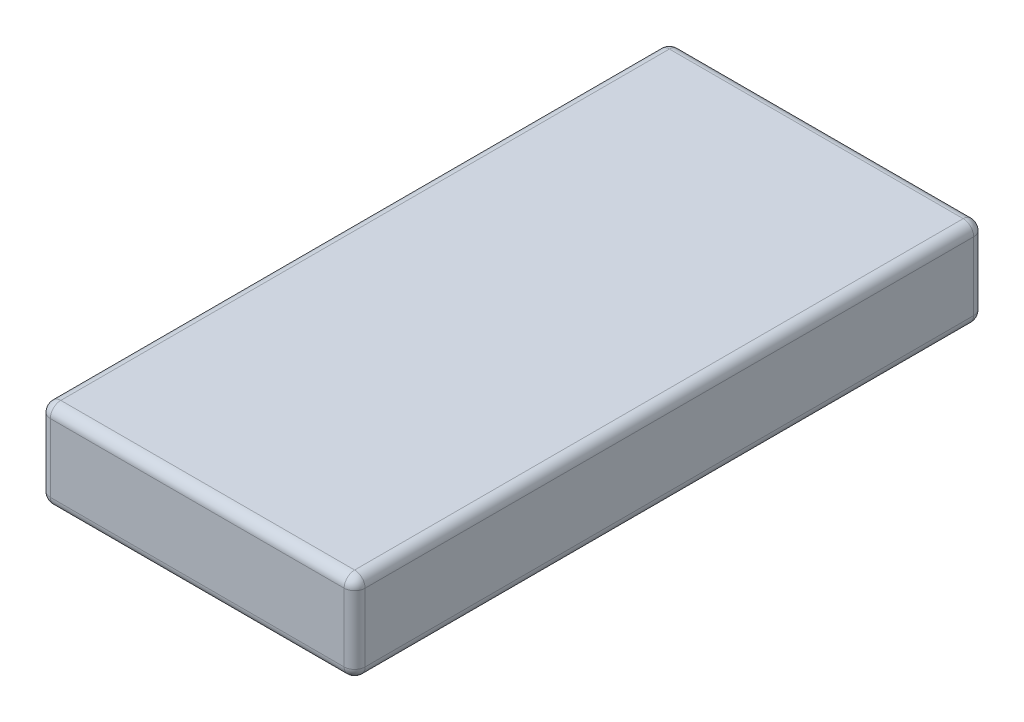
SolidWorks part; units mm, degrees
ref_plane "Plan de face" through (0, 0, 0) normal (0, 0, 1) x (1, 0, 0)
ref_plane "Plan de dessus" through (0, 0, 0) normal (0, 1, 0) x (1, 0, 0)
ref_plane "Plan de droite" through (0, 0, 0) normal (1, 0, 0) x (0, 0, -1)
sketch "Esquisse3" plane through (0, 0, 0) normal (0, 1, 0) x (1, 0, 0)
  line L1 (1.5, -3) -> (-1.5, -3)
  line L2 (1.5, -3) -> (1.5, 3)
  line L3 (1.5, 3) -> (-1.5, 3)
  line L4 (-1.5, -3) -> (-1.5, 3)
  line L5 (1.5, -3) -> (-1.5, 3) construction
  line L6 (1.5, 3) -> (-1.5, -3) construction
  point P0 (0, 0)
  dimension "D1" = 6
  dimension "D2" = 3
extrude "Boss.-Extru.2" add sketch "Esquisse3" along normal blind 0.85
fillet "Congé2" radius 0.1 12 edges at (0, 0, -3) (-1.5, 0.425, -3) (-1.5, 0, 0) (-1.5, 0.425, 3) (0, 0, 3) (1.5, 0.425, 3) (1.5, 0.425, -3) (1.5, 0, 0) (0, 0.85, -3) (-1.5, 0.85, 0) (0, 0.85, 3) (1.5, 0.85, 0)
